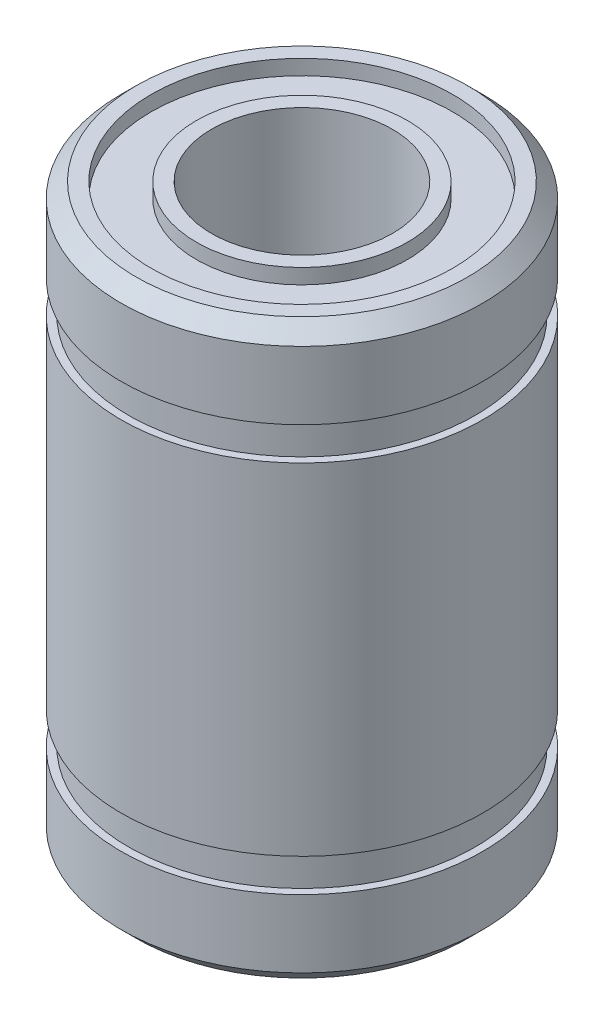
SolidWorks part; units mm, degrees
ref_plane "Front Plane" through (0, 0, 0) normal (0, 0, 1) x (1, 0, 0)
ref_plane "Top Plane" through (0, 0, 0) normal (0, 1, 0) x (1, 0, 0)
ref_plane "Right Plane" through (0, 0, 0) normal (1, 0, 0) x (0, 0, -1)
sketch "Sketch1" plane through (0, 0, 0) normal (0, 0, 1) x (1, 0, 0)
  line L0 (0, 9.5) -> (0, 0) construction
  line L1 (0, 0) -> (0, -9.5) construction
  line L2 (0, 9.5) -> (3, 9.5) construction
  line L3 (0, -9.5) -> (3, -9.5) construction
  line L4 (3, -9.5) -> (3, 9.5)
  line L5 (3, 9.5) -> (5.5, 9.5)
  line L6 (5.5, 9.5) -> (6, 9)
  line L7 (6, 9) -> (6, 6.75)
  line L8 (6, 5.65) -> (6, 6.75) construction
  line L9 (6, -6.75) -> (6, -5.65) construction
  line L10 (6, 5.65) -> (6, -5.65)
  line L11 (6, -9) -> (5.5, -9) construction
  line L12 (5.5, -9) -> (5.5, -9.5) construction
  line L13 (6, -6.75) -> (6, -9)
  line L14 (6, -9) -> (5.5, -9.5)
  line L15 (5.5, -9.5) -> (3, -9.5)
  line L16 (6, 9) -> (5.5, 9) construction
  line L17 (5.5, 9) -> (5.5, 9.5) construction
  line L18 (5.5, -9) -> (5.5, 9) construction
  line L19 (6.48, -6.2) -> (6.48, 6.2) construction
  line L20 (5.75, -6.2) -> (6.48, -6.2) construction
  line L21 (6, 6.75) -> (5.75, 6.75)
  line L22 (0, 0) -> (6, 0) construction
  line L23 (5.75, 6.75) -> (5.75, 5.65)
  line L24 (5.75, 5.65) -> (6, 5.65)
  line L25 (6, -5.65) -> (5.75, -5.65)
  line L26 (5.75, -5.65) -> (5.75, -6.75)
  line L27 (5.75, -6.75) -> (6, -6.75)
  arc A0 (6, 6.75) -> (6, 5.65) centre (6.48, 6.2) ccw construction
  arc A1 (6, -5.65) -> (6, -6.75) centre (6.48, -6.2) ccw construction
  dimension "Total_length" = 19
  dimension "Inside_diameter" = 6
  dimension "D4" = 0.5
  dimension "Distance_between_lockingrings" = 13.5
  dimension "Diameter_outside" = 12
  dimension "Locking_ring_width" = 1.1
  dimension "Locking_ring_groove_dia" = 11.5
revolve "Revolve1" add sketch "Sketch1" angle 360 about L0
sketch "Sketch2" plane through (0, 9.5, 0) normal (0, 1, 0) x (1, 0, 0)
  circle A0 centre (0, 0) radius 3.5
  circle A1 centre (0, 0) radius 5
  circle A2 centre (0, 0) radius 6 construction
  circle A3 centre (0, 0) radius 3 construction
  dimension "D1" = 1
  dimension "D2" = 0.5
extrude "Cut-Extrude1" cut sketch "Sketch2" against normal blind 0.5
mirror "Mirror1" about plane through (0, 0, 0) normal (0, 1, 0) of "Cut-Extrude1"
sketch "Sketch3" plane through (0, -9, 0) normal (0, -1, 0) x (1, 0, 0)
  line L0 (5, 0) -> (3.5, 0) construction
  circle A0 centre (0, 0) radius 3.85 construction
  circle A2 centre (0, 0) radius 5 construction
  circle A3 centre (0, 0) radius 3.5 construction
  text T0 "LM6UU" font "Century Gothic" height 0.8
  point P11 (4.25, 0)
  dimension "D1" = 0.4
split line "Split Line1"
